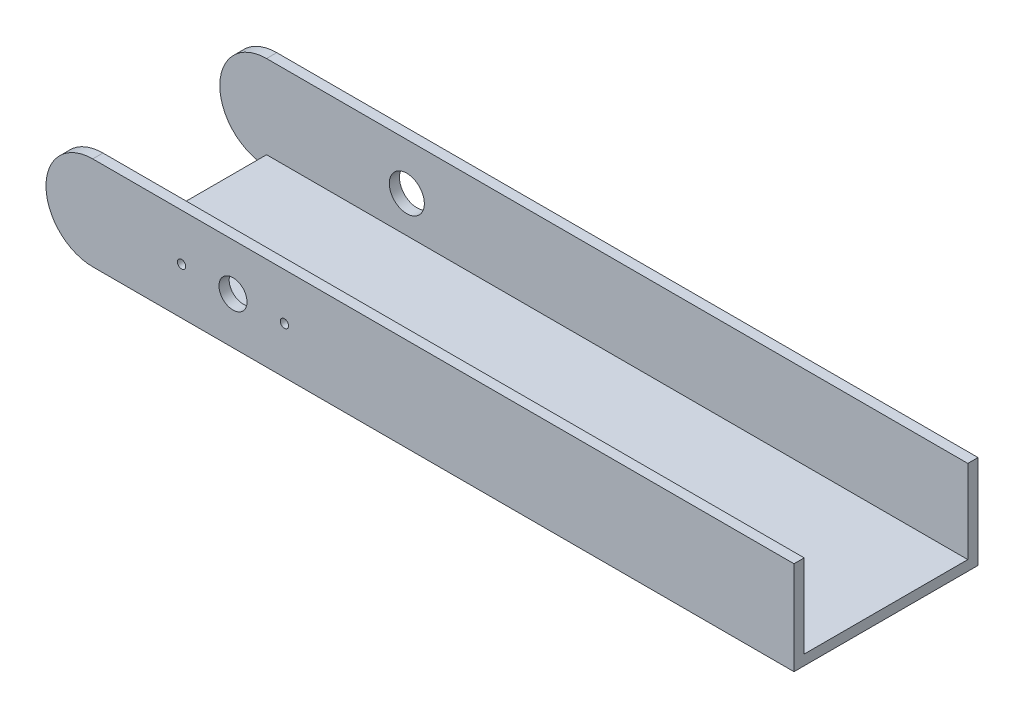
SolidWorks part; units mm, degrees
ref_plane "Front Plane" through (0, 0, 0) normal (0, 0, 1) x (1, 0, 0)
ref_plane "Top Plane" through (0, 0, 0) normal (0, 1, 0) x (1, 0, 0)
ref_plane "Right Plane" through (0, 0, 0) normal (1, 0, 0) x (0, 0, -1)
sketch "Sketch1" plane through (0, 0, 0) normal (0, 0, 1) x (1, 0, 0)
  line L1 (0, 0) -> (190.5, 0)
  line L3 (0, 25.4) -> (190.5, 25.4)
  line L4 (190.5, 0) -> (190.5, 25.4)
  arc A0 (0, 25.4) -> (0, 0) centre (0, 12.7) ccw
  point P6 (-12.7, 12.7)
  dimension "D3" = 12.7
  dimension "D1" = 203.2
  dimension "D2" = 25.4
extrude "Boss-Extrude1" add sketch "Sketch1" along normal blind 2.7686
sketch "Sketch3" plane through (0, 0, 2.7686) normal (0, 0, 1) x (1, 0, 0)
  line L0 (-12.7, 12.7) -> (190.5, 12.7) construction
  line L2 (190.5, 0) -> (190.5, 25.4) construction
  circle A0 centre (38.1, 12.7) radius 3.81
  arc A1 (0, 25.4) -> (0, 0) centre (0, 12.7) ccw construction
  circle A2 centre (24.13, 12.7) radius 1.1303
  circle A3 centre (52.07, 12.7) radius 1.1303
  dimension "D2" = 7.62
  dimension "D3" = 2.2606
  dimension "D4" = 2.2606
  dimension "D1" = 50.8
  dimension "D5" = 27.94
  dimension "D6" = 13.97
extrude "Cut-Extrude1" cut sketch "Sketch3" against normal through all
sketch "Sketch5" plane through (0, 0, 2.7686) normal (0, 0, 1) x (1, 0, 0)
  line L0 (190.5, 0) -> (190.5, 25.4) construction
  line L1 (0, 0) -> (190.5, 0)
  line L2 (0, 0) -> (0, 2.7686)
  line L3 (0, 2.7686) -> (190.5, 2.7686)
  line L4 (190.5, 0) -> (190.5, 2.7686)
  line L5 (0, 0) -> (190.5, 0) construction
  dimension "D1" = 2.7686
  dimension "D2" = 190.5
extrude "Boss-Extrude2" add sketch "Sketch5" against normal blind 44.45 from surface at -2.7686 starting at face at (25.2603, 12.7, 0)
sketch "Sketch6" plane through (0, 0, -44.45) normal (0, 0, -1) x (-1, 0, 0)
  line L0 (-190.5, 2.7686) -> (-190.5, 25.4) construction
  line L1 (12.7, 12.7) -> (-190.5, 12.7) construction
  line L3 (0, 25.4) -> (-190.5, 25.4)
  line L4 (-190.5, 12.7) -> (-190.5, 25.4)
  line L5 (-190.5, 12.7) -> (-190.5, 0)
  line L6 (-190.5, 0) -> (0, 0)
  arc A1 (0, 0) -> (0, 25.4) centre (0, 12.7) ccw construction
  arc A3 (0, 0) -> (0, 25.4) centre (0, 12.7) ccw construction
  arc A4 (0, 25.4) -> (0, 0) centre (0, 12.7) cw
extrude "Boss-Extrude3" add sketch "Sketch6" along normal blind 2.7686
sketch "Sketch7" plane through (0, 0, -47.2186) normal (0, 0, -1) x (-1, 0, 0)
  line L1 (-190.5, 12.7) -> (12.7, 12.7) construction
  line L2 (-190.5, 25.4) -> (-190.5, 0) construction
  arc A0 (0, 0) -> (0, 25.4) centre (0, 12.7) ccw construction
  circle A1 centre (-38.1, 12.7) radius 4.7625
  dimension "D1" = 9.525
  dimension "D2" = 50.8
extrude "Cut-Extrude2" cut sketch "Sketch7" against normal up to surface (2.7686 mm away) from surface at 0 up to face at (73.66, 11.2674, -44.45) starting at face at (92.075, 12.7, -47.2186)
